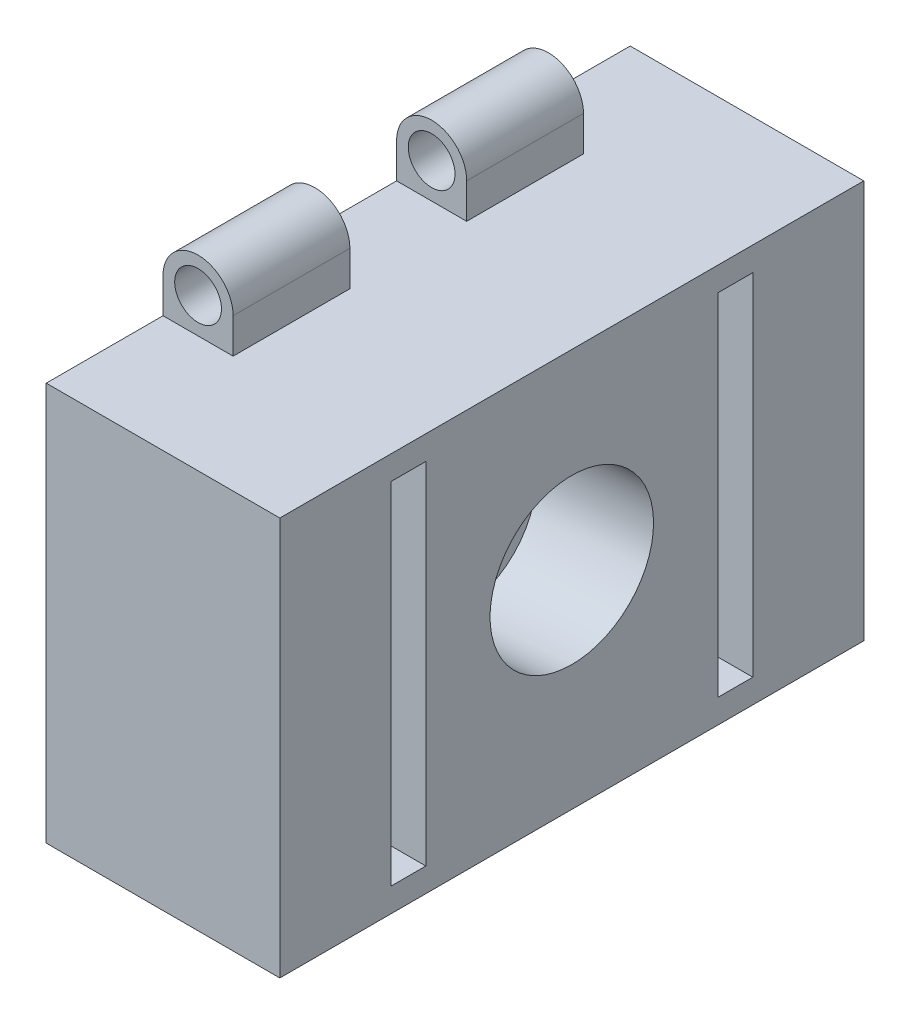
SolidWorks part; units mm, degrees
ref_plane "Front Plane" through (0, 0, 0) normal (0, 0, 1) x (1, 0, 0)
ref_plane "Top Plane" through (0, 0, 0) normal (0, 1, 0) x (1, 0, 0)
ref_plane "Right Plane" through (0, 0, 0) normal (1, 0, 0) x (0, 0, -1)
sketch "Sketch1" plane through (0, 0, 0) normal (1, 0, 0) x (0, 0, -1)
  line L1 (0, 0) -> (50, 0)
  line L2 (0, 0) -> (0, 34.11)
  line L3 (0, 34.11) -> (50, 34.11)
  line L4 (50, 0) -> (50, 34.11)
  dimension "D1" = 50
  dimension "D2" = 34.11
extrude "Boss-Extrude1" add sketch "Sketch1" along normal blind 20
sketch "Sketch2" plane through (0, 0, 0) normal (0, 0, 1) x (1, 0, 0)
  line L0 (3, 37.11) -> (3, 34.11) construction
  line L1 (20, 34.11) -> (0, 34.11) construction
  line L2 (0, 34.11) -> (0, 37.11)
  line L3 (0, 34.11) -> (3, 34.11)
  line L4 (3, 34.11) -> (6, 34.11)
  line L5 (6, 34.11) -> (6, 37.11)
  line L6 (6, 37.11) -> (3, 37.11) construction
  circle A0 centre (3, 37.11) radius 2
  arc A1 (6, 37.11) -> (0, 37.11) centre (3, 37.11) ccw
  dimension "D1" = 4
  dimension "D2" = 3
  dimension "D3" = 3
ref_plane "Plane1" through (0, 0, -10) normal (0, 0, 1) x (1, 0, 0)
sketch "Sketch3" plane through (0, 0, -10) normal (0, 0, 1) x (1, 0, 0)
  line L0 (3, 37.11) -> (3, 34.11) construction
  line L2 (0, 34.11) -> (0, 37.11)
  line L3 (0, 34.11) -> (3, 34.11)
  line L4 (3, 34.11) -> (6, 34.11)
  line L5 (6, 34.11) -> (6, 37.11)
  line L6 (6, 37.11) -> (3, 37.11) construction
  line L7 (0, 34.11) -> (0, 0) construction
  line L8 (20, 34.11) -> (0, 34.11) construction
  circle A0 centre (3, 37.11) radius 2
  arc A1 (6, 37.11) -> (0, 37.11) centre (3, 37.11) ccw
  dimension "D1" = 4
  dimension "D2" = 3
  dimension "D3" = 3
extrude "Boss-Extrude2" add sketch "Sketch3" against normal blind 10
pattern_linear "LPattern1" count 2 spacing 20 along (0, 0, -1) of "Boss-Extrude2"
ref_plane "Plane2" through (0, 17.055, 0) normal (0, 1, 0) x (1, 0, 0)
mirror "Mirror1" about plane through (0, 17.055, 0) normal (0, 1, 0) of "LPattern1", "Boss-Extrude2"
ref_plane "Plane3" through (0, 0, -25) normal (0, 0, 1) x (1, 0, 0)
sketch "Sketch4" plane through (0, 0, -25) normal (0, 0, 1) x (1, 0, 0)
  line L0 (20, 17.055) -> (0, 17.055) construction
  line L1 (20, 34.11) -> (20, 0) construction
  line L2 (0, 34.11) -> (0, 0) construction
  line L3 (10, 0) -> (10, 34.11) construction
  line L4 (20, 0) -> (0, 0) construction
  line L5 (20, 34.11) -> (0, 34.11) construction
  line L6 (10, 17.055) -> (20, 17.7543) construction
  dimension "D1" = 4
ref_plane "Plane4" through (20, 17.7543, -25) normal (0.9976, 0.0698, 0) x (0, 0, -1)
sketch "Sketch5" plane through (20, 17.7543, -25) normal (0.9976, 0.0698, 0) x (0, 0, -1)
  line L0 (0, -17.0135) -> (0, 17.0135) construction
  line L6 (0, 0) -> (0, 16.3159) construction
  line L7 (25, 16.3159) -> (-25, 16.3159) construction
  circle A0 centre (0, 0) radius 7
  point P4 (0, 0)
  point P7 (0, 0)
  dimension "D1" = 14
extrude "Cut-Extrude1" cut sketch "Sketch5" against normal blind 10 and the other way up to next
sketch "Sketch6" plane through (20, 0, 0) normal (1, 0, 0) x (0, 0, -1)
  line L0 (25, 34.11) -> (25, 0) construction
  line L1 (50, 34.11) -> (0, 34.11) construction
  line L2 (0, 0) -> (50, 0) construction
  line L3 (12.5, 17.055) -> (37.5, 17.055)
  line L4 (12.5, 2.055) -> (12.5, 32.055)
  line L5 (12.5, 32.055) -> (9.5, 32.055)
  line L6 (9.5, 32.055) -> (9.5, 2.055)
  line L7 (9.5, 2.055) -> (12.5, 2.055)
  line L8 (40.5, 32.055) -> (40.5, 2.055)
  line L9 (37.5, 32.055) -> (40.5, 32.055)
  line L10 (37.5, 2.055) -> (37.5, 32.055)
  line L11 (40.5, 2.055) -> (37.5, 2.055)
  point P9 (25, 17.055)
  point P12 (12.5, 17.055)
  dimension "D1" = 25
  dimension "D2" = 30
  dimension "D3" = 3
extrude "Cut-Extrude2" cut sketch "Sketch6" against normal blind 10 contours L6 L7 L4 L5 | L11 L8 L9 L10
